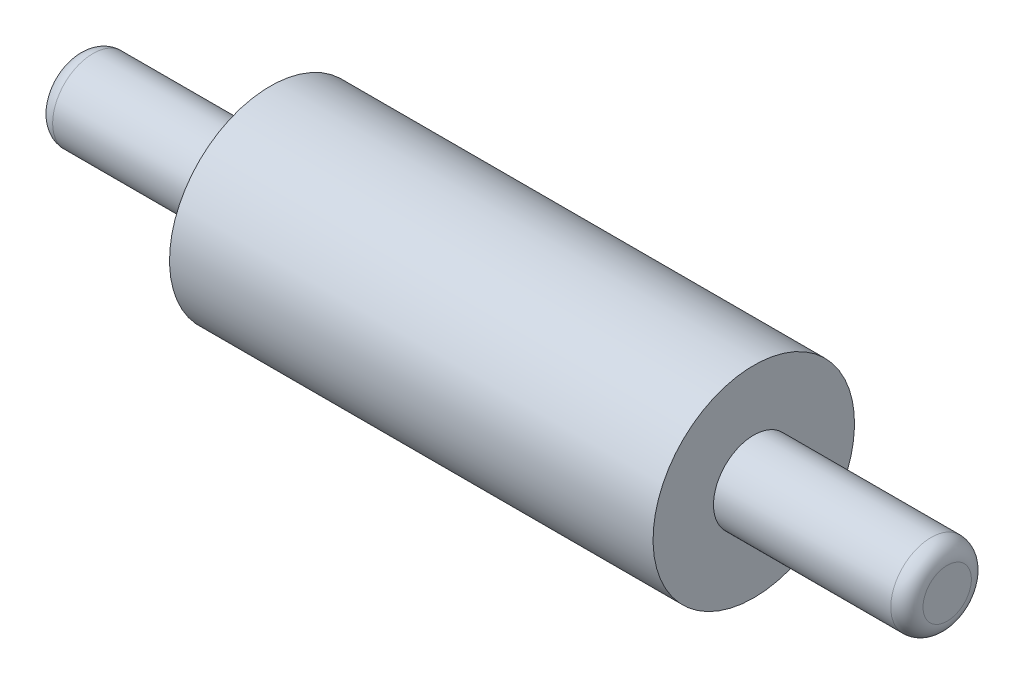
SolidWorks part; units mm, degrees
ref_plane "Front Plane" through (0, 0, 0) normal (0, 0, 1) x (1, 0, 0)
ref_plane "Top Plane" through (0, 0, 0) normal (0, 1, 0) x (1, 0, 0)
ref_plane "Right Plane" through (0, 0, 0) normal (1, 0, 0) x (0, 0, -1)
sketch "Sketch1" plane through (0, 0, 0) normal (0, 0, 1) x (1, 0, 0)
  line L0 (-68.58, 0) -> (68.58, 0)
  line L1 (68.58, 0) -> (68.58, 6.35)
  line L2 (68.58, 6.35) -> (38.1, 6.35)
  line L3 (38.1, 6.35) -> (38.1, 15.875)
  line L4 (38.1, 15.875) -> (-38.1, 15.875)
  line L5 (-38.1, 15.875) -> (-38.1, 6.35)
  line L6 (-38.1, 6.35) -> (-68.58, 6.35)
  line L7 (-68.58, 6.35) -> (-68.58, 0)
  dimension "D1" = 137.16
  dimension "D2" = 76.2
  dimension "D3" = 6.35
  dimension "D4" = 9.525
revolve "Revolve2" add sketch "Sketch1" angle 360 about L0
fillet "Fillet1" radius 2.54 2 edges at (-68.58, -6.35, 0) (68.58, -6.35, 0)
